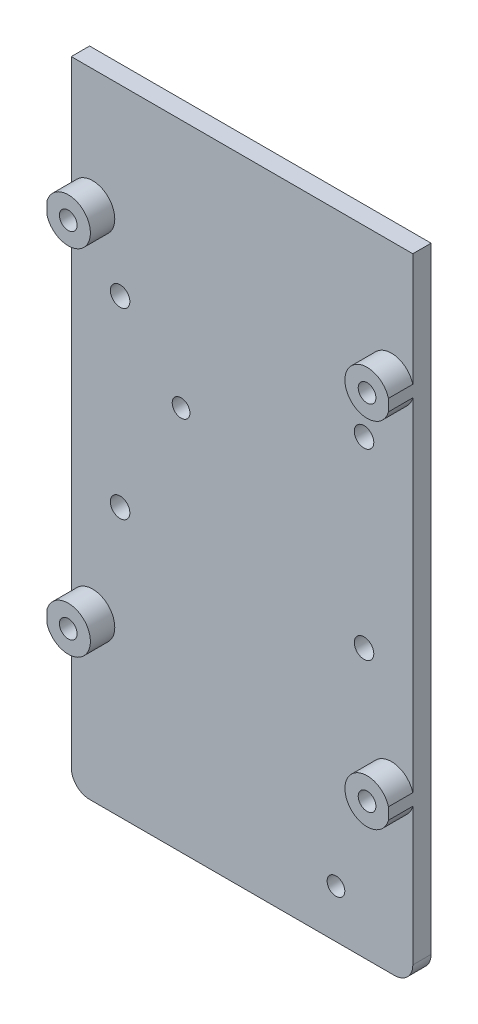
SolidWorks part; units mm, degrees
ref_plane "Front Plane" through (0, 0, 0) normal (0, 0, 1) x (1, 0, 0)
ref_plane "Top Plane" through (0, 0, 0) normal (0, 1, 0) x (1, 0, 0)
ref_plane "Right Plane" through (0, 0, 0) normal (1, 0, 0) x (0, 0, -1)
sketch "Sketch2" plane through (0, 0, 0) normal (0, 0, 1) x (1, 0, 0)
  line L0 (-15.1668, -33.2317) -> (-15.1668, -38.1317) construction
  line L1 (-15.1668, -33.2317) -> (-2.5668, -33.2317) construction
  line L2 (-40.5668, 21.9683) -> (-40.5668, -38.1317) construction
  line L3 (-40.5668, 21.9683) -> (-2.5668, 21.9683) construction
  line L4 (-55.5668, -38.1317) -> (-5.5668, -38.1317)
  line L5 (-2.5668, -35.1317) -> (-2.5668, 65.8683)
  line L6 (-58.5668, 65.8683) -> (-58.5668, -35.1317)
  line L7 (-55.5668, -38.1317) -> (-5.5668, -38.1317) construction
  line L8 (-2.5668, -35.1317) -> (-2.5668, 65.8683) construction
  line L9 (-2.5668, 65.8683) -> (-58.5668, 65.8683)
  line L10 (-58.5668, 65.8683) -> (-58.5668, -35.1317) construction
  line L11 (-30.5668, -38.1317) -> (-30.5668, 46.8683) construction
  line L12 (-58.5668, 46.8683) -> (-2.5668, 46.8683) construction
  line L13 (-30.5668, 65.8683) -> (-30.5668, 10.8683) construction
  line L14 (-30.5668, 10.8683) -> (-2.5668, 10.8683) construction
  arc A1 (-5.5668, -38.1317) -> (-2.5668, -35.1317) centre (-5.5668, -35.1317) ccw
  arc A2 (-58.5668, -35.1317) -> (-55.5668, -38.1317) centre (-55.5668, -35.1317) ccw
  circle A3 centre (-15.1668, -33.2317) radius 1.25 construction
  circle A4 centre (-40.5668, 21.9683) radius 1.25 construction
  arc A5 (-5.5668, -38.1317) -> (-2.5668, -35.1317) centre (-5.5668, -35.1317) ccw construction
  arc A6 (-58.5668, -35.1317) -> (-55.5668, -38.1317) centre (-55.5668, -35.1317) ccw construction
extrude "Boss-Extrude1" add sketch "Sketch2" along normal blind 3
sketch "Sketch3" plane through (0, 0, 3) normal (0, 0, 1) x (1, 0, 0)
  line L0 (-30.5668, 65.8683) -> (-50.5668, 65.8683) construction
  line L1 (-2.5668, 65.8683) -> (-58.5668, 65.8683) construction
  line L2 (-50.5668, 65.8683) -> (-50.5668, 35.8683) construction
  line L3 (-2.5668, 47.3683) -> (-2.5668, 43.8683) construction
  line L4 (-50.5668, 35.8683) -> (-50.5668, 5.8683) construction
  line L5 (-30.5668, 65.8683) -> (-30.5668, 46.8683) construction
  line L7 (-2.5668, 43.8683) -> (-6.0668, 43.8683) construction
  line L8 (-6.0668, 43.8683) -> (-6.0668, -14.1317) construction
  line L9 (-6.0668, -14.1317) -> (-6.0668, -37.6317) construction
  line L11 (-55.0668, 46.3683) -> (-58.5668, 46.3683) construction
  line L12 (-58.5668, 65.8683) -> (-58.5668, -35.1317) construction
  line L13 (-55.0668, -11.6317) -> (-58.5668, -11.6317) construction
  circle A0 centre (-50.5668, 35.8683) radius 1.6
  circle A1 centre (-50.5668, 5.8683) radius 1.6
  circle A2 centre (-10.5668, 5.8683) radius 1.6
  circle A3 centre (-10.5668, 35.8683) radius 1.6
  circle A4 centre (-40.5668, 24.9683) radius 1.45
  circle A5 centre (-15.1668, -30.2317) radius 1.45
  circle A6 centre (-6.0668, 46.3683) radius 1.45
  circle A7 centre (-6.0668, -11.6317) radius 1.45
  circle A8 centre (-55.0668, -11.6317) radius 1.45
  circle A9 centre (-55.0668, 46.3683) radius 1.45
extrude "Cut-Extrude1" cut sketch "Sketch3" against normal through all
sketch "Sketch4" plane through (0, 0, 3) normal (0, 0, 1) x (1, 0, 0)
  line L4 (-55.5668, -38.1317) -> (-5.5668, -38.1317)
  line L5 (-2.5668, -35.1317) -> (-2.5668, 65.8683)
  line L6 (-2.5668, 65.8683) -> (-58.5668, 65.8683)
  line L7 (-58.5668, 65.8683) -> (-58.5668, -35.1317)
  line L8 (-55.5668, -38.1317) -> (-5.5668, -38.1317)
  line L9 (-2.5668, -35.1317) -> (-2.5668, 65.8683)
  line L10 (-2.5668, 65.8683) -> (-58.5668, 65.8683)
  line L11 (-58.5668, 65.8683) -> (-58.5668, -35.1317)
  circle A0 centre (-55.0668, 46.3683) radius 1.45 construction
  circle A1 centre (-55.0668, -11.6317) radius 1.45 construction
  arc A2 (-58.5668, -35.1317) -> (-55.5668, -38.1317) centre (-55.5668, -35.1317) ccw
  arc A3 (-5.5668, -38.1317) -> (-2.5668, -35.1317) centre (-5.5668, -35.1317) ccw
  arc A4 (-58.5668, -35.1317) -> (-55.5668, -38.1317) centre (-55.5668, -35.1317) ccw
  arc A5 (-5.5668, -38.1317) -> (-2.5668, -35.1317) centre (-5.5668, -35.1317) ccw
  circle A6 centre (-6.0668, 46.3683) radius 1.45 construction
  circle A8 centre (-6.0668, -11.6317) radius 1.45 construction
  circle A10 centre (-55.0668, 46.3683) radius 1.45
  circle A11 centre (-55.0668, -11.6317) radius 1.45
  circle A12 centre (-6.0668, 46.3683) radius 1.45
  circle A13 centre (-40.5668, 24.9683) radius 1.45
  circle A14 centre (-6.0668, -11.6317) radius 1.45
  circle A15 centre (-15.1668, -30.2317) radius 1.25
  circle A16 centre (-55.0668, 46.3683) radius 3.6293
  circle A17 centre (-40.5668, 24.9683) radius 3.5
  circle A18 centre (-55.0668, -11.6317) radius 3.6293
  circle A19 centre (-15.1668, -30.2317) radius 3.5
  circle A20 centre (-6.0668, -11.6317) radius 3.6293
  circle A21 centre (-6.0668, 46.3683) radius 3.6293
  circle M7 centre (-55.0668, 46.3683) radius 1.45
  circle M8 centre (-55.0668, -11.6317) radius 1.45
  circle M9 centre (-6.0668, -11.6317) radius 1.45
  circle M10 centre (-6.0668, 46.3683) radius 1.45
  dimension "D1" = 0
extrude "Boss-Extrude2" add sketch "Sketch4" along normal blind 4 contours L11 A18 M8 | L11 A16 M7 | L9 A20 M9 | L9 A21 M10
